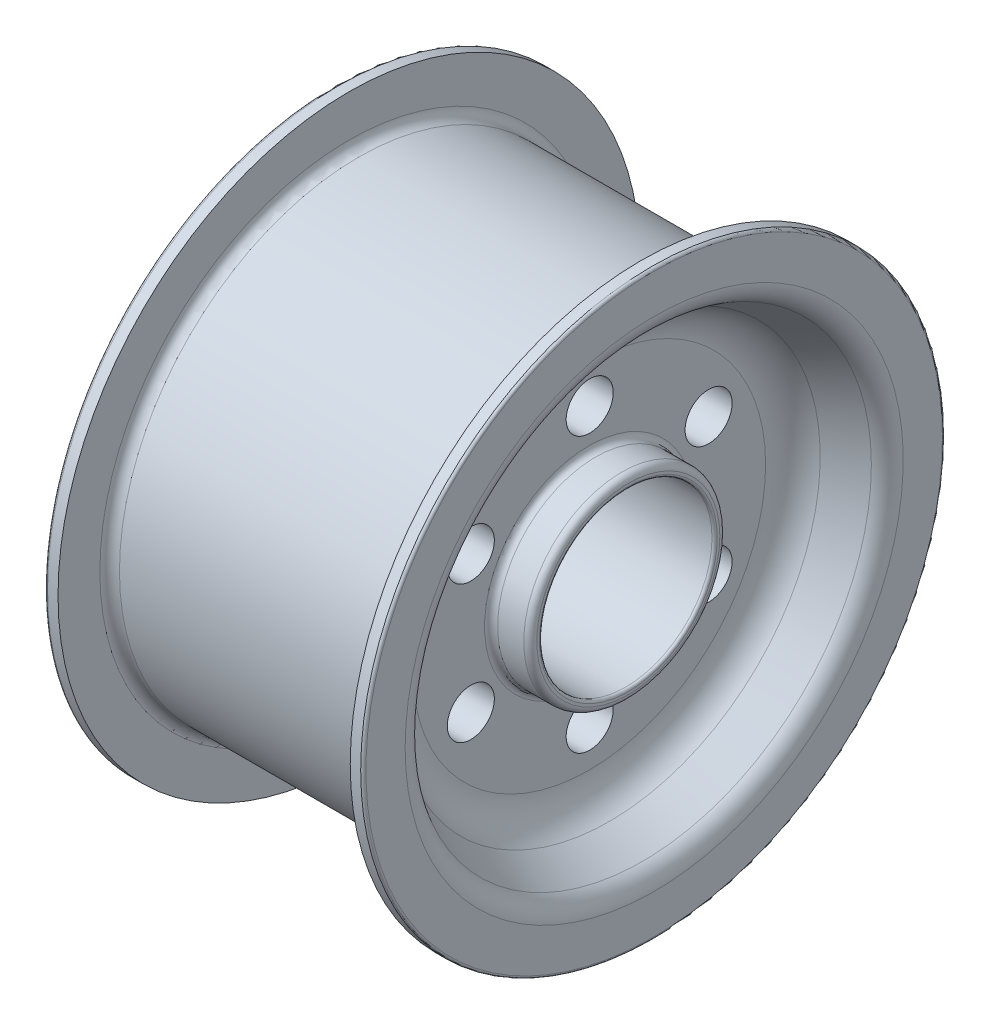
SolidWorks part; units mm, degrees
ref_plane "Front Plane" through (0, 0, 0) normal (0, 0, 1) x (1, 0, 0)
ref_plane "Top Plane" through (0, 0, 0) normal (0, 1, 0) x (1, 0, 0)
ref_plane "Right Plane" through (0, 0, 0) normal (1, 0, 0) x (0, 0, -1)
sketch "Sketch1" plane through (0, 0, 0) normal (0, 0, 1) x (1, 0, 0)
  line L0 (-111.76, 222.5) -> (-111.76, 190.5)
  line L1 (-72, 135) -> (-72, 75)
  line L2 (-111.76, 222.5) -> (-121.76, 222.5)
  line L3 (-121.76, 222.5) -> (-121.76, 190.5)
  line L4 (-104.26, 183) -> (104.26, 183)
  line L5 (-112.7153, 175.1782) -> (-87.5051, 161.2659)
  line L6 (-72, 75) -> (-102, 75)
  line L7 (-102, 75) -> (-102, 0)
  line L8 (-102, 0) -> (102, 0)
  line L9 (111.76, 222.5) -> (111.76, 190.5)
  line L10 (121.76, 222.5) -> (121.76, 190.5)
  line L11 (111.76, 222.5) -> (121.76, 222.5)
  line L12 (112.7153, 175.1782) -> (87.5051, 161.2659)
  line L13 (72, 75) -> (102, 75)
  line L14 (72, 135) -> (72, 75)
  line L15 (102, 75) -> (102, 0)
  line L16 (0, 0) -> (162.7004, 0) construction
  arc A0 (-111.76, 190.5) -> (-104.26, 183) centre (-104.26, 190.5) ccw
  arc A1 (-121.76, 190.5) -> (-112.7153, 175.1782) centre (-104.26, 190.5) ccw
  arc A2 (-87.5051, 161.2659) -> (-72, 135) centre (-102, 135) cw
  arc A3 (111.76, 190.5) -> (104.26, 183) centre (104.26, 190.5) cw
  arc A4 (121.76, 190.5) -> (112.7153, 175.1782) centre (104.26, 190.5) cw
  arc A5 (87.5051, 161.2659) -> (72, 135) centre (102, 135) ccw
  point P15 (0, 183)
  point P27 (0, 0)
  line B0 (0, 0) -> (111.76, 0) construction
  line B1 (0, 0) -> (0, 190.5) construction
  line B2 (0, 190.5) -> (111.76, 190.5) construction
  line B3 (0, 190.5) -> (0, 381) construction
  line B4 (96.76, 190.5) -> (96.76, 236.9265)
  line B5 (111.76, 190.5) -> (111.76, 236.9265)
  line B6 (0, 190.5) -> (41.7248, 378.7084) construction
  line B7 (0, 190.5) -> (58.6334, 376.4613) construction
  line B8 (-96.76, 190.5) -> (-96.76, 236.9265)
  line B9 (-111.76, 190.5) -> (-111.76, 236.9265)
  arc B10 (111.76, 190.5) -> (96.76, 190.5) centre (104.26, 190.5) cw
  arc B11 (-72.286, 374.0799) -> (-63.5687, 375.6595) centre (0, 0) cw
  arc B12 (-69.4401, 359.3523) -> (69.4401, 359.3523) centre (0, 0) cw
  arc B13 (72.286, 374.0799) -> (120.8373, 288.3152) centre (60, 310.5) cw
  arc B14 (120.8373, 288.3152) -> (111.76, 236.9265) centre (261.76, 236.9265) ccw
  arc B15 (69.4401, 359.3523) -> (106.745, 293.454) centre (60, 310.5) cw
  arc B16 (106.745, 293.454) -> (96.76, 236.9265) centre (261.76, 236.9265) ccw
  arc B17 (36.7514, 379.2233) -> (46.691, 378.1282) centre (41.7248, 378.7084) ccw
  arc B18 (53.688, 377.1984) -> (63.5687, 375.6595) centre (58.6334, 376.4613) ccw
  arc B19 (-53.688, 377.1984) -> (-63.5687, 375.6595) centre (-58.6334, 376.4613) cw
  arc B20 (-36.7514, 379.2233) -> (-46.691, 378.1282) centre (-41.7248, 378.7084) cw
  arc B21 (-53.688, 377.1984) -> (-46.691, 378.1282) centre (0, 0) cw
  arc B22 (-36.7514, 379.2233) -> (36.7514, 379.2233) centre (0, 0) cw
  arc B23 (46.691, 378.1282) -> (53.688, 377.1984) centre (0, 0) cw
  arc B24 (63.5687, 375.6595) -> (72.286, 374.0799) centre (0, 0) cw
  arc B25 (-111.76, 190.5) -> (-96.76, 190.5) centre (-104.26, 190.5) ccw
  arc B26 (-72.286, 374.0799) -> (-120.8373, 288.3152) centre (-60, 310.5) ccw
  arc B27 (-69.4401, 359.3523) -> (-106.745, 293.454) centre (-60, 310.5) ccw
  arc B28 (-106.745, 293.454) -> (-96.76, 236.9265) centre (-261.76, 236.9265) cw
  arc B29 (-120.8373, 288.3152) -> (-111.76, 236.9265) centre (-261.76, 236.9265) cw
  dimension "D1" = 222.5
sketch_block_instance "Blok1-1"
sketch_block "Blok1" parameters "D3"=7.5, "D6"=5, "D7"=5, "D9"=366, "D12"=165, "D1"=111.76, "D2"=190.5, "D4"=12.5, "D5"=5, "D8"=381, "D10"=60, "D11"=120, "D13"=60
revolve "Revolve1" add sketch "Sketch1" angle 360 about L16
sketch "Sketch2" plane through (72, 0, 0) normal (1, 0, 0) x (0, 0, -1)
  circle A0 centre (0.4482, 106.0086) radius 18
  circle A1 centre (91.3809, 53.5086) radius 18
  circle A2 centre (91.3809, -51.4914) radius 18
  circle A3 centre (0.4482, -103.9914) radius 18
  circle A4 centre (-90.4845, -51.4914) radius 18
  circle A5 centre (-90.4845, 53.5086) radius 18
  point P12 (0, 0)
extrude "Cut-Extrude1" cut sketch "Sketch2" against normal through all
sketch "Sketch3" plane through (102, 0, 0) normal (1, 0, 0) x (0, 0, -1)
  circle A0 centre (0, 0) radius 66
extrude "Cut-Extrude2" cut sketch "Sketch3" against normal through all
fillet "Fillet1" radius 5 2 edges at (102, 0, 75) (72, 0, 75)
fillet "Fillet2" radius 2 2 edges at (-121.76, 0, 222.5) (121.76, 0, 222.5)
fillet "Fillet3" radius 5 2 edges at (-72, 0, 75) (-102, 0, 75)
fillet "Fillet4" radius 2 2 edges at (-102, 0, -66) (102, 0, -66)
scale "Scale1" scale about centroid uniform scaling yes scale factor 1.09591
sketch "Sketch4" plane through (133.438, 0, 0) normal (1, 0, 0) x (0, 0, -1)
  line L0 (0.0025, 243.8455) -> (0.0025, -243.8345)
  circle A0 centre (0.0025, 0.0055) radius 243.84 construction
